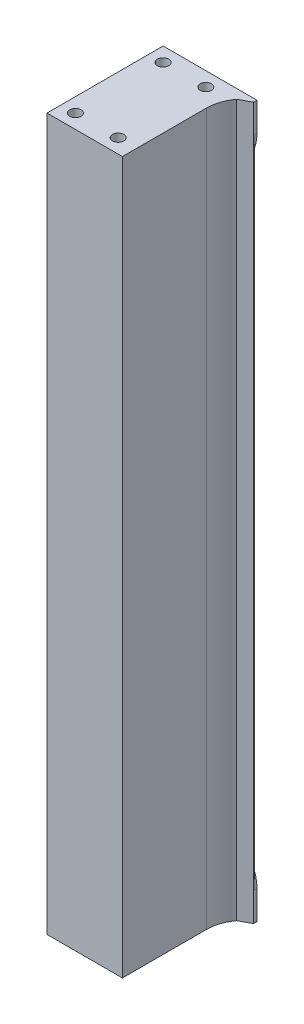
SolidWorks part; units mm, degrees
ref_plane "Front Plane" through (0, 0, 0) normal (0, 0, 1) x (1, 0, 0)
ref_plane "Top Plane" through (0, 0, 0) normal (0, 1, 0) x (1, 0, 0)
ref_plane "Right Plane" through (0, 0, 0) normal (1, 0, 0) x (0, 0, -1)
sketch "Sketch1" plane through (0, 0, 0) normal (0, 1, 0) x (1, 0, 0)
  line L0 (6.5, 9.5) -> (6.5, -20)
  line L1 (20, -20) -> (-20, -20) construction
  line L2 (20, -20) -> (20, 20) construction
  line L3 (20, 20) -> (-20, 20) construction
  line L4 (-20, -20) -> (-20, 20) construction
  line L5 (0, 20) -> (0, -20) construction
  line L6 (20, 0) -> (-20, 0) construction
  line L7 (6.5, -20) -> (-20, -20)
  line L8 (-20, -20) -> (-20, 20)
  line L9 (-20, 20) -> (13, 20)
  line L10 (13, 20) -> (13, 19.6)
  line L11 (9.1257, 17.5) -> (13, 19.6)
  circle A0 centre (20, 9.5) radius 10.5 construction
  circle A1 centre (20, 9.5) radius 13.5 construction
  arc A2 (6.5, 9.5) -> (9.1257, 17.5) centre (20, 9.5) cw
  point P0 (0, 0)
  dimension "D1" = 21
  dimension "D2" = 40
  dimension "D3" = 40
  dimension "D5" = 0.4
  dimension "D6" = 7
  dimension "D7" = 8
  dimension "D4" = 3
extrude "Boss-Extrude1" add sketch "Sketch1" along normal blind 250
sketch "Sketch2" plane through (0, 0, -20) normal (0, 0, -1) x (-1, 0, 0)
  line L0 (20, 250) -> (20, 0) construction
  line L1 (53, 25) -> (-13, 25) construction
  line L2 (53, 25) -> (53, 225) construction
  line L3 (53, 225) -> (-13, 225) construction
  line L4 (-13, 25) -> (-13, 225) construction
  line L5 (20, 225) -> (20, 25) construction
  line L6 (53, 125) -> (-13, 125) construction
  line L7 (-13, 250) -> (-13, 0) construction
  line L8 (20, 225) -> (20, 250)
  line L9 (20, 250) -> (-13, 250)
  line L10 (-13, 250) -> (-13, 240)
  line L11 (2, 225) -> (20, 225)
  line L12 (-13, 0) -> (-13, 10)
  line L13 (20, 0) -> (-13, 0)
  line L14 (20, 25) -> (20, 0)
  line L15 (2, 25) -> (20, 25)
  arc A0 (-13, 240) -> (2, 225) centre (2, 240) ccw
  arc A1 (-13, 10) -> (2, 25) centre (2, 10) cw
  point P0 (20, 125)
  dimension "D2" = 15
  dimension "D1" = 200
extrude "Boss-Extrude2" add sketch "Sketch2" along normal blind 0.8
sketch "Sketch3" plane through (0, 0, 0) normal (0, -1, 0) x (1, 0, 0)
  line L0 (-20, 20) -> (6.5, 20) construction
  line L1 (0, -15.8) -> (-15, -15.8) construction
  line L2 (0, -15.8) -> (0, 15) construction
  line L3 (0, 15) -> (-15, 15) construction
  line L4 (-15, -15.8) -> (-15, 15) construction
  line L5 (-7.5, 15) -> (-7.5, -15.8) construction
  line L6 (0, -0.4) -> (-15, -0.4) construction
  line L7 (-20, -20.8) -> (-20, 20) construction
  line L8 (13, -20.8) -> (-20, -20.8) construction
  circle A0 centre (-15, 15) radius 2
  circle A1 centre (0, 15) radius 2
  circle A2 centre (0, -15.8) radius 2
  circle A3 centre (-15, -15.8) radius 2
  point P0 (-7.5, -0.4)
  dimension "D5" = 4
  dimension "D1" = 5
  dimension "D2" = 5
  dimension "D3" = 5
  dimension "D4" = 15
extrude "Cut-Extrude2" cut sketch "Sketch3" against normal blind 8
ref_plane "Plane1" through (0, 125, 0) normal (0, 1, 0) x (1, 0, 0)
mirror "Mirror1" about plane through (0, 125, 0) normal (0, 1, 0) of "Cut-Extrude2"
fillet "Fillet1" radius 5 1 edges at (-20, 125, -20)
sketch "Sketch4" plane through (0, 0, -20.8) normal (0, 0, -1) x (-1, 0, 0)
  line L1 (20, 250) -> (5, 250) construction
  line L2 (20, 250) -> (20, 240) construction
  line L3 (20, 240) -> (5, 240) construction
  line L4 (5, 250) -> (5, 240) construction
  line L5 (12.5, 240) -> (12.5, 250) construction
  line L6 (20, 245) -> (5, 245) construction
  circle A0 centre (5, 240) radius 2
  point P336 (12.5, 245)
  dimension "D3" = 4
  dimension "D1" = 10
  dimension "D2" = 15
extrude "Cut-Extrude3" cut sketch "Sketch4" against normal blind 8
mirror "Mirror2" about plane through (0, 125, 0) normal (0, 1, 0) of "Cut-Extrude3"
